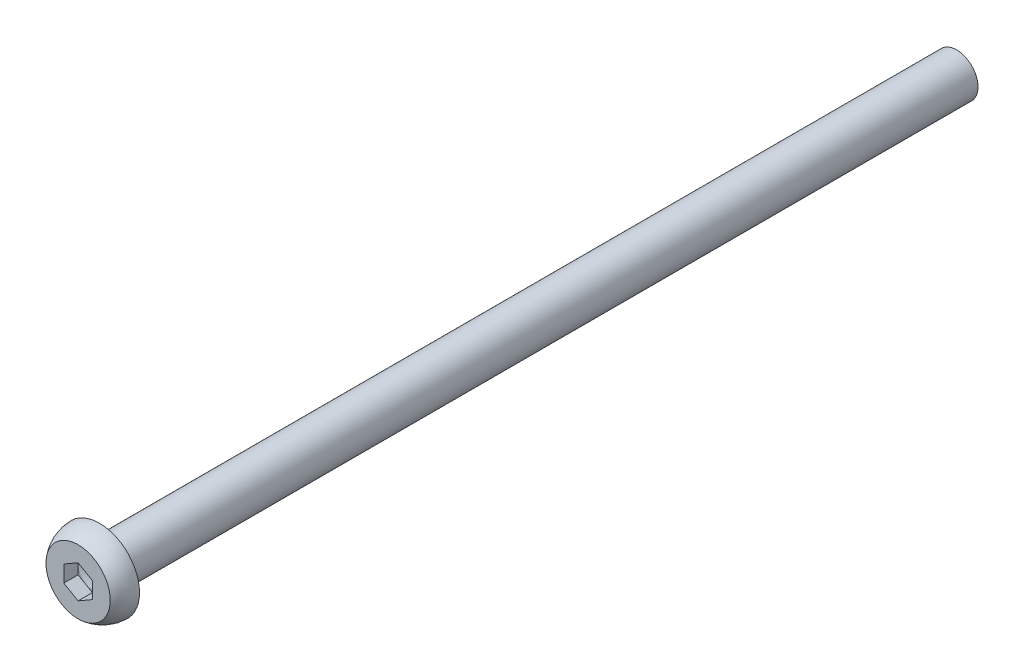
SolidWorks part; units mm, degrees
ref_plane "前视基准面" through (0, 0, 0) normal (0, 0, 1) x (1, 0, 0)
ref_plane "上视基准面" through (0, 0, 0) normal (0, 1, 0) x (1, 0, 0)
ref_plane "右视基准面" through (0, 0, 0) normal (1, 0, 0) x (0, 0, -1)
sketch "草图1" plane through (0, 0, 0) normal (1, 0, 0) x (0, 0, -1)
  line L4 (0, 2.2503) -> (0, 1)
  line L6 (1, 1) -> (1.2482, 0)
  line L12 (1.5, 2.8) -> (1.5, 1.5)
  line L13 (0, 0) -> (1.5, 0) construction
  line L15 (0, 1) -> (0, 0)
  line L16 (0, 0) -> (1, 0)
  line L17 (1, 0) -> (1, 1)
  line L23 (1.5, 1.5) -> (1.5, 0)
  line L24 (1.5, 0) -> (1.2482, 0)
  arc A0 (1.5, 2.8) -> (0, 2.2503) centre (1.5, 0.4784) ccw
revolve "旋转1" add sketch "草图1" angle 360 about L13
sketch "草图2" plane through (0, 0, 0) normal (0, 0, 1) x (1, 0, 0)
  line L1 (0, 1.1547) -> (-1, 0.5774)
  line L2 (-1, 0.5774) -> (-1, -0.5774)
  line L3 (-1, -0.5774) -> (0, -1.1547)
  line L4 (0, -1.1547) -> (1, -0.5774)
  line L5 (1, -0.5774) -> (1, 0.5774)
  line L6 (1, 0.5774) -> (0, 1.1547)
  circle A0 centre (0, 0) radius 1 construction
  dimension "D1" = 2
extrude "切除-拉伸2" cut sketch "草图2" against normal blind 1
sketch "草图3" plane through (0, 0, -1.5) normal (0, 0, -1) x (-1, 0, 0)
  circle A0 centre (0, 0) radius 1.5
extrude "凸台-拉伸1" add sketch "草图3" along normal blind 60
